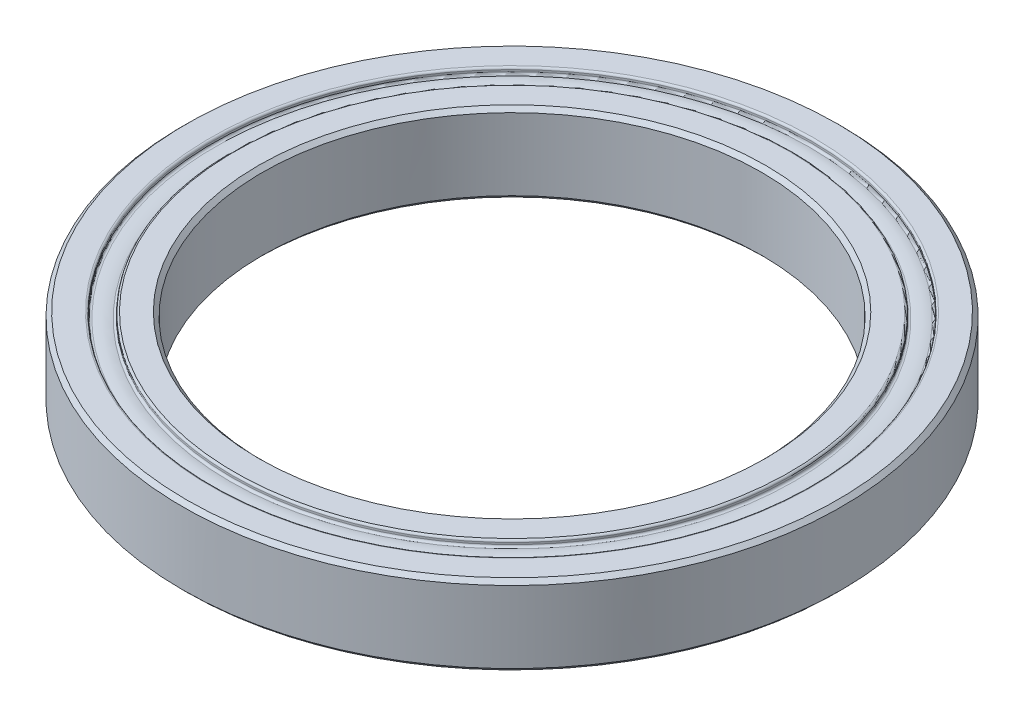
SolidWorks part; units mm, degrees
material "201 退火不锈钢 (SS)"
ref_plane "前视基准面" through (0, 0, 0) normal (0, 0, 1) x (1, 0, 0)
ref_plane "上视基准面" through (0, 0, 0) normal (0, 1, 0) x (1, 0, 0)
ref_plane "右视基准面" through (0, 0, 0) normal (1, 0, 0) x (0, 0, -1)
sketch "草图1" plane through (0, 0, 0) normal (0, 0, 1) x (1, 0, 0)
  line L0 (0, 0) -> (0, 8) construction
  line L1 (-25, 8) -> (-25, 0)
  line L2 (-25, 0) -> (-27.8, 0)
  line L3 (-33, 0) -> (-33, 8)
  line L4 (-33, 8) -> (-30.2, 8)
  line L5 (-33, 4) -> (-25, 4) construction
  line L6 (-27.8, 8) -> (-25, 8)
  line L8 (-28, 0.2) -> (-28, 0.3875)
  line L10 (-30, 0.2) -> (-30, 0.3875)
  line L11 (-28, 0) -> (-30, 8) construction
  line L12 (-28, 8) -> (-30, 0) construction
  line L13 (-30, 7.6125) -> (-30, 7.8)
  line L14 (-28, 7.6125) -> (-28, 7.8)
  line L15 (-30.2, 0) -> (-33, 0)
  arc A0 (-29.7568, 0.5828) -> (-28.2432, 0.5828) centre (-29, 4) ccw
  arc A1 (-28.2432, 7.4172) -> (-29.7568, 7.4172) centre (-29, 4) ccw
  arc A2 (-28.2432, 0.5828) -> (-28, 0.3875) centre (-28.2, 0.3875) cw
  arc A3 (-28.2432, 7.4172) -> (-28, 7.6125) centre (-28.2, 7.6125) ccw
  arc A4 (-29.7568, 0.5828) -> (-30, 0.3875) centre (-29.8, 0.3875) ccw
  arc A5 (-29.7568, 7.4172) -> (-30, 7.6125) centre (-29.8, 7.6125) cw
  arc A6 (-30.2, 0) -> (-30, 0.2) centre (-30.2, 0.2) ccw
  arc A7 (-28, 7.8) -> (-27.8, 8) centre (-27.8, 7.8) cw
  arc A8 (-27.8, 0) -> (-28, 0.2) centre (-27.8, 0.2) cw
  arc A9 (-30.2, 8) -> (-30, 7.8) centre (-30.2, 7.8) cw
  point P22 (-28, 7.3541)
  point P27 (-30, 7.3541)
  dimension "D4" = 7
  dimension "D6" = 0.2
  dimension "D1" = 50
  dimension "D2" = 8
  dimension "D3" = 8
  dimension "D5" = 2
revolve "旋转1" add sketch "草图1" angle 360 about L0
chamfer "倒角1" distance 0.4 angle 45 4 edges at (0, 8, -33) (0, 8, -25) (0, 0, -25) (0, 0, -33)
move or copy body "实体-移动/复制1" [suppressed] bodies to move or copy 106
